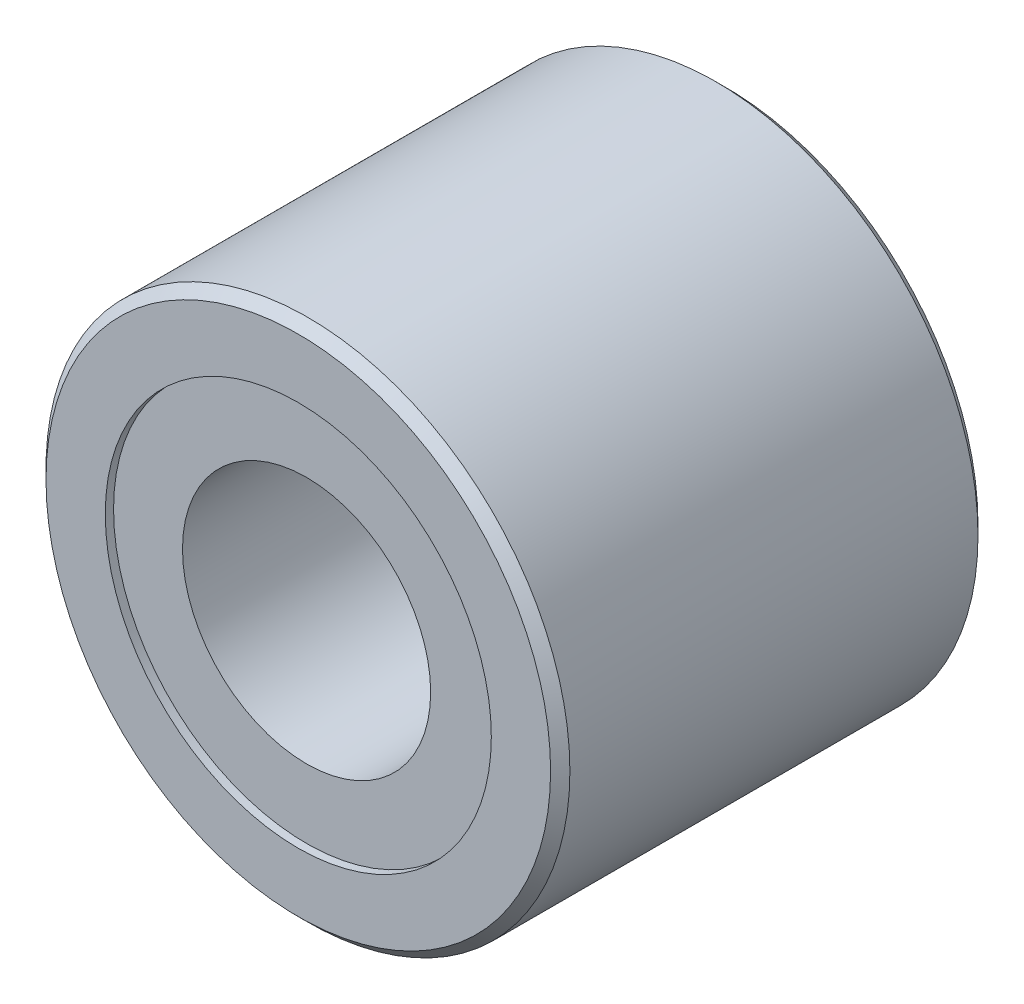
SolidWorks part; units mm, degrees
ref_plane "Piano frontale" through (0, 0, 0) normal (0, 0, 1) x (1, 0, 0)
ref_plane "Piano superiore" through (0, 0, 0) normal (0, 1, 0) x (1, 0, 0)
ref_plane "Piano destro" through (0, 0, 0) normal (1, 0, 0) x (0, 0, -1)
sketch "Schizzo1" plane through (0, 0, 0) normal (0, 0, 1) x (1, 0, 0)
  circle A0 centre (0, 0) radius 9.5
  circle A1 centre (0, 0) radius 7
extrude "Estrusione-Estrusione2" add sketch "Schizzo1" along normal blind 15.5
ref_plane "Piano1" through (0, 0, 0.3) normal (0, 0, -1) x (-1, 0, 0)
sketch "Schizzo2" plane through (0, 0, 0.3) normal (0, 0, -1) x (-1, 0, 0)
  circle A0 centre (0, 0) radius 7
  circle A1 centre (0, 0) radius 4.5
extrude "Estrusione-Estrusione3" add sketch "Schizzo2" against normal blind 14.9
chamfer "Smusso1" distance 0.35 angle 45 2 edges at (9.5, 0, 15.5) (9.5, 0, 0)
sketch "Schizzo3" plane through (0, 0, 0) normal (0, 1, 0) x (1, 0, 0)
  line L0 (0, 0) -> (0, -15.5)
  line L1 (10.065, -0.3) -> (-10.065, -0.3) construction
  point P2 (0, -7.75)
